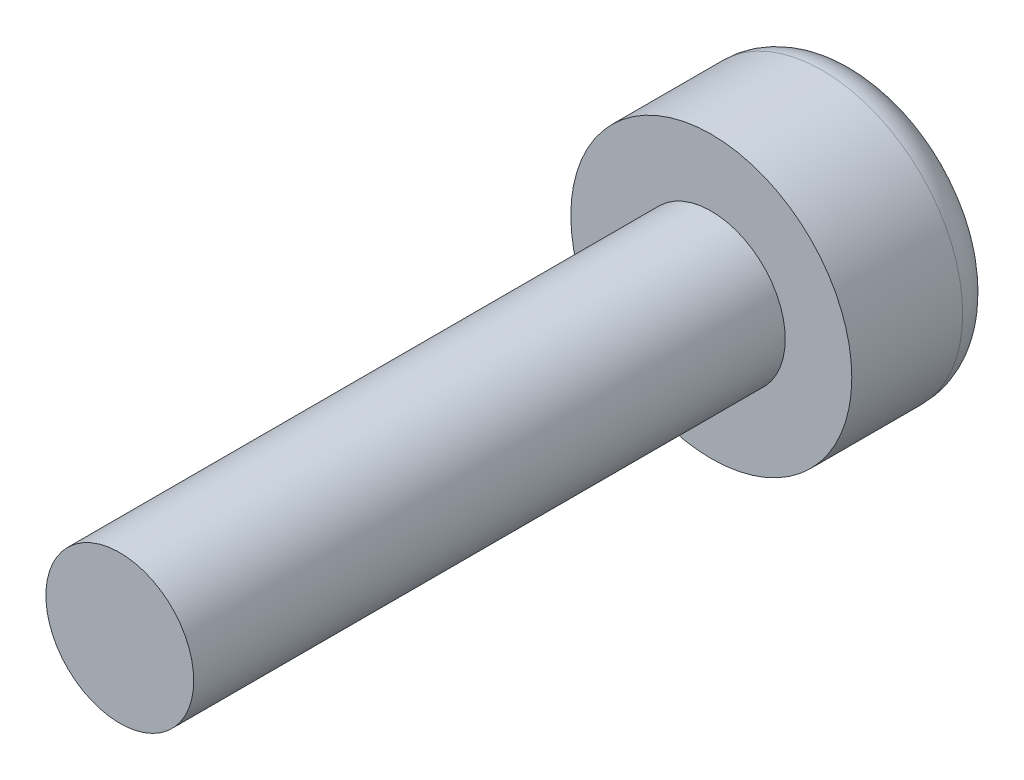
SolidWorks part; units mm, degrees
ref_plane "正面" through (0, 0, 0) normal (0, 0, 1) x (1, 0, 0)
ref_plane "平面" through (0, 0, 0) normal (0, 1, 0) x (1, 0, 0)
ref_plane "右側面" through (0, 0, 0) normal (1, 0, 0) x (0, 0, -1)
sketch "ｽｹｯﾁ2" plane through (0, 0, 0) normal (0, 0, 1) x (1, 0, 0)
  circle A0 centre (0, 0) radius 1.9
  dimension "D1" = 3.8
extrude "ﾎﾞｽ - 押し出し1" add sketch "ｽｹｯﾁ2" along normal blind 2
sketch "ｽｹｯﾁ3" plane through (0, 0, 2) normal (0, 0, 1) x (1, 0, 0)
  circle A0 centre (0, 0) radius 1
  dimension "D1" = 2
extrude "ﾎﾞｽ - 押し出し2" add sketch "ｽｹｯﾁ3" along normal blind 8
fillet "ﾌｨﾚｯﾄ1" radius 0.5 1 edges at (1.9, 0, 0)
